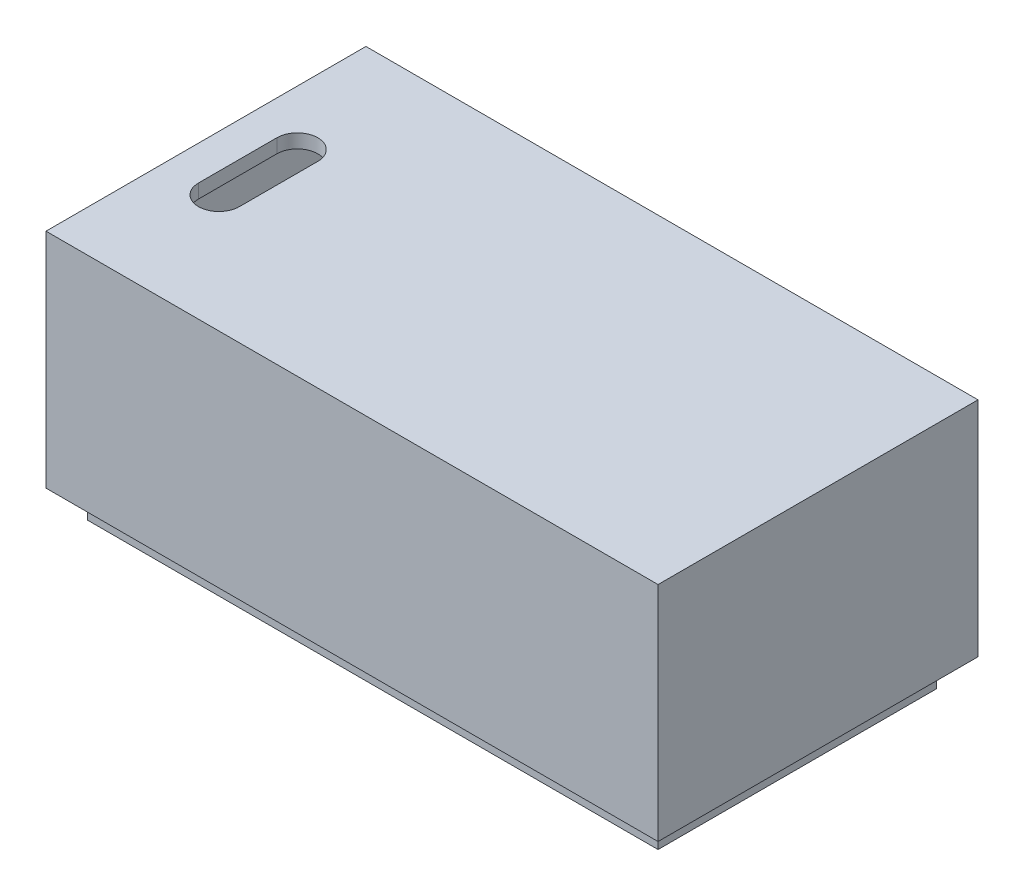
SolidWorks part; units mm, degrees
ref_plane "Front Plane" through (0, 0, 0) normal (0, 0, 1) x (1, 0, 0)
ref_plane "Top Plane" through (0, 0, 0) normal (0, 1, 0) x (1, 0, 0)
ref_plane "Right Plane" through (0, 0, 0) normal (1, 0, 0) x (0, 0, -1)
sketch "Sketch3" plane through (0, 0, 0) normal (0, 1, 0) x (1, 0, 0)
  line L1 (0, 0) -> (55.88, 0)
  line L2 (0, 0) -> (0, 29.21)
  line L3 (0, 29.21) -> (55.88, 29.21)
  line L4 (55.88, 0) -> (55.88, 29.21)
extrude "Boss-Extrude4" add sketch "Sketch3" along normal blind 20.32
sketch "Sketch5" plane through (0, 0, -29.21) normal (0, 0, -1) x (-1, 0, 0)
  line L14 (-1.27, 1.27) -> (-1.27, 19.05)
  line L15 (-54.61, 1.27) -> (-1.27, 1.27)
  line L16 (-54.61, 19.05) -> (-54.61, 1.27)
  line L17 (-1.27, 19.05) -> (-54.61, 19.05)
  line L18 (-1.27, 1.27) -> (-1.27, 19.05)
  line L19 (-54.61, 1.27) -> (-1.27, 1.27)
  line L20 (-54.61, 19.05) -> (-54.61, 1.27)
  line L21 (-1.27, 19.05) -> (-54.61, 19.05)
  dimension "D1" = 1.27
extrude "Cut-Extrude1" cut sketch "Sketch5" against normal blind 27.94 contours L18 L21 L20 L19
sketch "Sketch6" plane through (0, 20.32, 0) normal (0, 1, 0) x (1, 0, 0)
  line L0 (5.0215, 17.9251) -> (5.0215, 10.7691) construction
  line L1 (6.8911, 17.9251) -> (6.8911, 10.7691)
  line L2 (3.1519, 17.9251) -> (3.1519, 10.7691)
  arc A0 (6.8911, 17.9251) -> (3.1519, 17.9251) centre (5.0215, 17.9251) ccw
  arc A1 (3.1519, 10.7691) -> (6.8911, 10.7691) centre (5.0215, 10.7691) ccw
  point P2 (5.0215, 14.3471)
  point P13 (0, 0)
extrude "Cut-Extrude2" cut sketch "Sketch6" against normal up to next
sketch "Sketch7" plane through (0, 0, 0) normal (0, -1, 0) x (1, 0, 0)
  line L21 (53.975, -27.305) -> (53.975, -1.905)
  line L22 (1.905, -27.305) -> (53.975, -27.305)
  line L23 (1.905, -1.905) -> (1.905, -27.305)
  line L24 (53.975, -1.905) -> (1.905, -1.905)
  line L25 (53.975, -27.305) -> (53.975, -1.905)
  line L26 (1.905, -27.305) -> (53.975, -27.305)
  line L27 (1.905, -1.905) -> (1.905, -27.305)
  line L28 (53.975, -1.905) -> (1.905, -1.905)
  dimension "D2" = 1.905
extrude "Boss-Extrude5" add sketch "Sketch7" along normal blind 2.54 contours L25 L28 L27 L26
sketch "Sketch8" plane through (1.905, 0, 0) normal (-1, 0, 0) x (0, 0, 1)
  line L16 (-26.543, 0) -> (-2.667, 0)
  line L19 (-2.667, 0) -> (-2.667, -1.778)
  line L20 (-2.667, -1.778) -> (-26.543, -1.778)
  line L21 (-26.543, -1.778) -> (-26.543, 0)
  line L22 (-2.667, 0) -> (-2.667, -1.778)
  line L23 (-2.667, -1.778) -> (-26.543, -1.778)
  line L24 (-26.543, -1.778) -> (-26.543, 0)
  dimension "D1" = 0.762
extrude "Cut-Extrude3" cut sketch "Sketch8" against normal up to next
